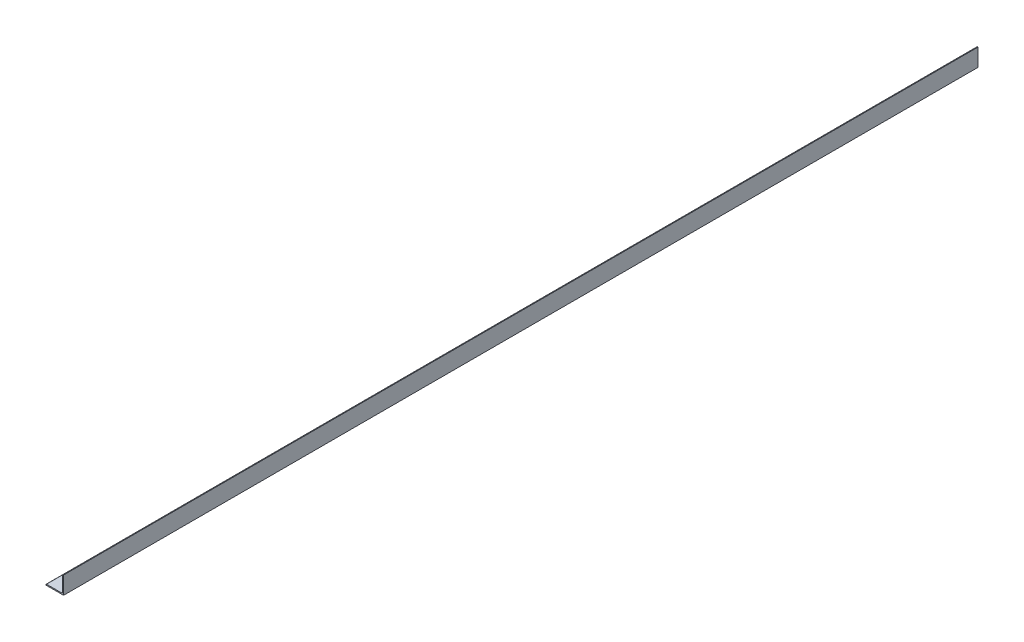
SolidWorks part; units mm, degrees
ref_plane "Front Plane" through (0, 0, 0) normal (0, 0, 1) x (1, 0, 0)
ref_plane "Top Plane" through (0, 0, 0) normal (0, 1, 0) x (1, 0, 0)
ref_plane "Right Plane" through (0, 0, 0) normal (1, 0, 0) x (0, 0, -1)
sketch "Sketch0" plane through (0, 0, 0) normal (0, 0, 1) x (1, 0, 0)
  line L0 (-12.7, -12.7) -> (12.7, -12.7)
  line L1 (12.7, -12.7) -> (12.7, 12.7)
  line L2 (12.7, 0) -> (0, 0) construction
  line L3 (0, 0) -> (0, -12.7) construction
  line L4 (11.1125, -9.5377) -> (11.1125, 12.7) construction
  line L5 (9.5377, -11.1125) -> (-12.7, -11.1125) construction
  arc A0 (11.1125, -9.5377) -> (9.5377, -11.1125) centre (9.5377, -9.5377) cw
  point P3 (10.6513, -10.6513)
  dimension "Inside Corner Radius" = 1.5748
  dimension "Outside Height" = 25.4
  dimension "Inside Height" = 23.8125
  dimension "Inside Width" = 23.8125
  dimension "Wall Thickness" = 1.5875
  dimension "D1" = 1.5875
  dimension "Outside Width" = 25.4
sketch "Sketch1" plane through (0, 0, 0) normal (1, 0, 0) x (0, 0, -1)
  line L0 (609.6, 0) -> (-609.6, 0)
  point P4 (0, 0)
  dimension "Length" = 1219.2
sketch "Sketch2" plane through (0, 0, 0) normal (0, 0, 1) x (1, 0, 0)
  line L0 (-12.7, -12.7) -> (12.7, -12.7)
  line L1 (12.7, -12.7) -> (12.7, 12.7)
  line L2 (12.7, 12.7) -> (11.1125, 12.7) construction
  line L3 (11.1125, 11.9062) -> (11.1125, -9.5377)
  line L4 (9.5377, -11.1125) -> (-11.9062, -11.1125)
  line L5 (-12.7, -12.7) -> (-12.7, -11.1125) construction
  line L6 (11.9062, 12.7) -> (12.7, 12.7)
  line L7 (-12.7, -11.9062) -> (-12.7, -12.7)
  line L8 (12.7, 0) -> (0, 0) construction
  line L9 (0, 0) -> (0, -12.7) construction
  arc A0 (11.1125, 11.9062) -> (11.9062, 12.7) centre (11.9062, 11.9062) cw
  arc A1 (-12.7, -11.9062) -> (-11.9062, -11.1125) centre (-11.9062, -11.9062) cw
  arc A2 (11.1125, -9.5377) -> (9.5377, -11.1125) centre (9.5377, -9.5377) cw
  dimension "Inside Radius" = 1.5748
  dimension "Height" = 25.4
  dimension "Width" = 25.4
  dimension "Thickness" = 1.5875
extrude "Boss-Extrude1" add sketch "Sketch2" along normal mid plane 1320.8
sketch "Break Locations" plane through (0, 0, 0) normal (1, 0, 0) x (0, 0, -1)
  line L0 (-634.492, 0) -> (634.492, 0)
  line L1 (-660.4, -12.7) -> (-660.4, 12.7) construction
  line L2 (660.4, -12.7) -> (660.4, 12.7) construction
  point P0 (-638.81, 0)
  point P1 (638.81, 0)
  point P10 (0, 0)
  point P11 (634.492, 0)
  point P13 (-634.492, 0)
  dimension "D1" = 21.59
  dimension "D2" = 21.59
  dimension "D3" = 25.908
equation "\"D1@Break Locations\" = .85 * \"Height@Sketch2\""
equation "\"D2@Break Locations\"=\"D1@Break Locations\""
equation "\"Thickness@Sketch2\"=\"wall thickness@sketch0\""
equation "\"Height@Sketch2\"=\"outside height@sketch0\""
equation "\"Width@Sketch2\"=\"outside width@sketch0\""
equation "\"Inside Radius@Sketch2\"=\"inside corner radius@sketch0\""
equation "\"D3@Break Locations\"=\"D2@Break Locations\"*1.2"
equation "\"D1@Sketch0\"=\"Wall Thickness@Sketch0\""
